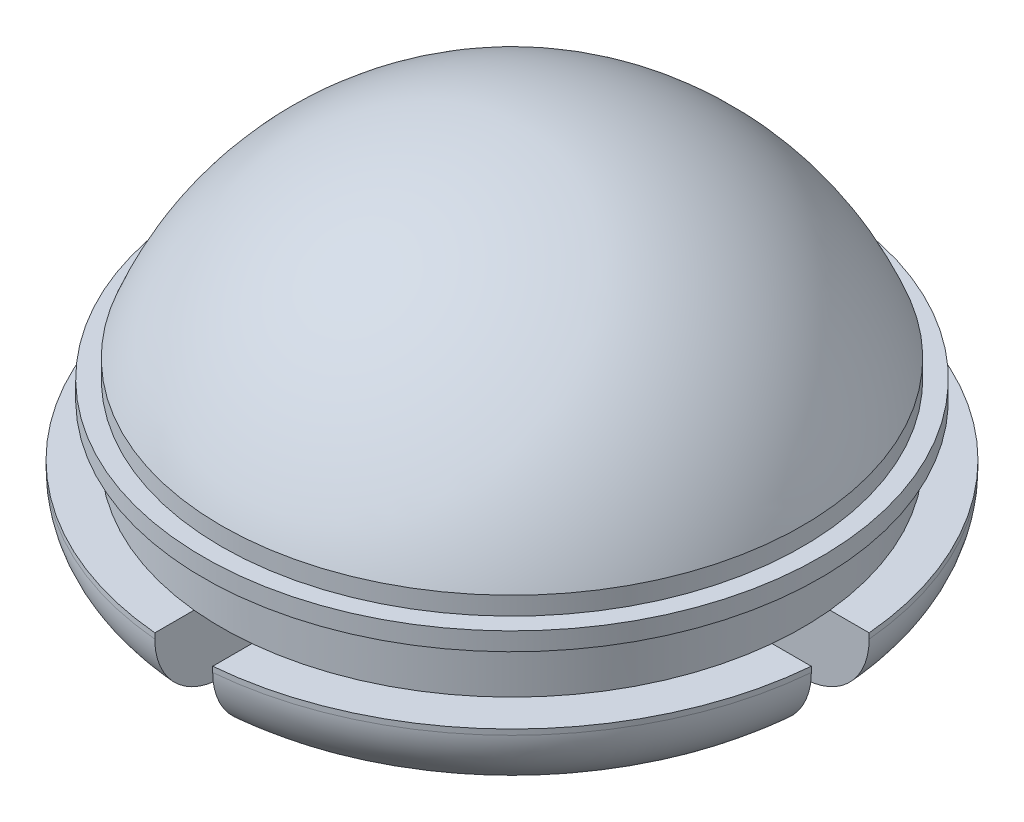
SolidWorks part; units mm, degrees
ref_plane "Front Plane" through (0, 0, 0) normal (0, 0, 1) x (1, 0, 0)
ref_plane "Top Plane" through (0, 0, 0) normal (0, 1, 0) x (1, 0, 0)
ref_plane "Right Plane" through (0, 0, 0) normal (1, 0, 0) x (0, 0, -1)
sketch "Sketch1" plane through (0, 0, 0) normal (0, 0, 1) x (1, 0, 0)
  line L0 (0, 0) -> (0, 1.0242) construction
  line L1 (0, 0.0003) -> (-3.6082, 0.0003) construction
  line L2 (-8.03, -5.5597) -> (-8.03, -6.0597)
  line L3 (-8.03, -6.0597) -> (-8.53, -6.0597)
  line L4 (-8.53, -6.0597) -> (-8.53, -6.5597)
  line L5 (-8.53, -6.5597) -> (-8.03, -6.5597)
  line L6 (-8.03, -6.5597) -> (-8.03, -7.9997)
  line L7 (-8.03, -7.9997) -> (-9.11, -7.9997)
  line L8 (-9.11, -7.9997) -> (-9.11, -8.1497)
  line L9 (-7.26, -9.9997) -> (-5.86, -9.9997)
  line L10 (-5.36, -9.4997) -> (-5.36, -6.4486)
  line L11 (0, -2.8097) -> (0, 0)
  arc A0 (0, 0) -> (-8.03, -5.5597) centre (0.0771, -8.6902) ccw
  arc A1 (-5.36, -6.4486) -> (0, -2.8097) centre (0.0771, -8.6902) cw
  arc A2 (-9.11, -8.1497) -> (-7.26, -9.9997) centre (-7.26, -8.1497) ccw
  arc A3 (-5.86, -9.9997) -> (-5.36, -9.4997) centre (-5.86, -9.4997) ccw
  point P20 (-9.11, -9.9997)
  point P21 (0, 0)
  dimension "D5" = 1.85
  dimension "D12" = 0.5
  dimension "D1" = 0.5
  dimension "D2" = 0.5
  dimension "D3" = 1.44
  dimension "D4" = 2
  dimension "D6" = 1.08
  dimension "D7" = 0.5
  dimension "D8" = 8.03
  dimension "D9" = 10
  dimension "D10" = 3.75
  dimension "D11" = 7.19
revolve "Revolve1" add sketch "Sketch1" angle 360 about L0
sketch "Sketch2" plane through (0, -9.9997, 0) normal (0, -1, 0) x (1, 0, 0)
  line L0 (0, 0) -> (0, 14.1603) construction
  line L1 (0, 0) -> (-18.0239, 0) construction
  line L2 (-0.8, 0.8) -> (-0.8, 10.2345)
  line L3 (-0.8, 10.2345) -> (0.8, 10.2345)
  line L4 (0.8, 10.2345) -> (0.8, 0.8)
  line L5 (0.8, 0.8) -> (9.9517, 0.8)
  line L6 (9.9517, 0.8) -> (9.9517, -0.8)
  line L7 (9.9517, -0.8) -> (0.8, -0.8)
  line L8 (0.8, -0.8) -> (0.8, -9.8637)
  line L9 (0.8, -9.8637) -> (-0.8, -9.8637)
  line L10 (-0.8, -9.8637) -> (-0.8, -0.8)
  line L11 (-0.8, -0.8) -> (-10.7172, -0.8)
  line L12 (-10.7172, -0.8) -> (-10.7172, 0.8)
  line L13 (-10.7172, 0.8) -> (-0.8, 0.8)
  point P2 (0, 7.0801)
  dimension "D1" = 0.8
  dimension "D2" = 1.6
  dimension "D3" = 0.8
  dimension "D4" = 0.8
extrude "Cut-Extrude1" cut sketch "Sketch2" against normal up to surface (2 mm away) up to face at (0, -7.9997, -9.11)
